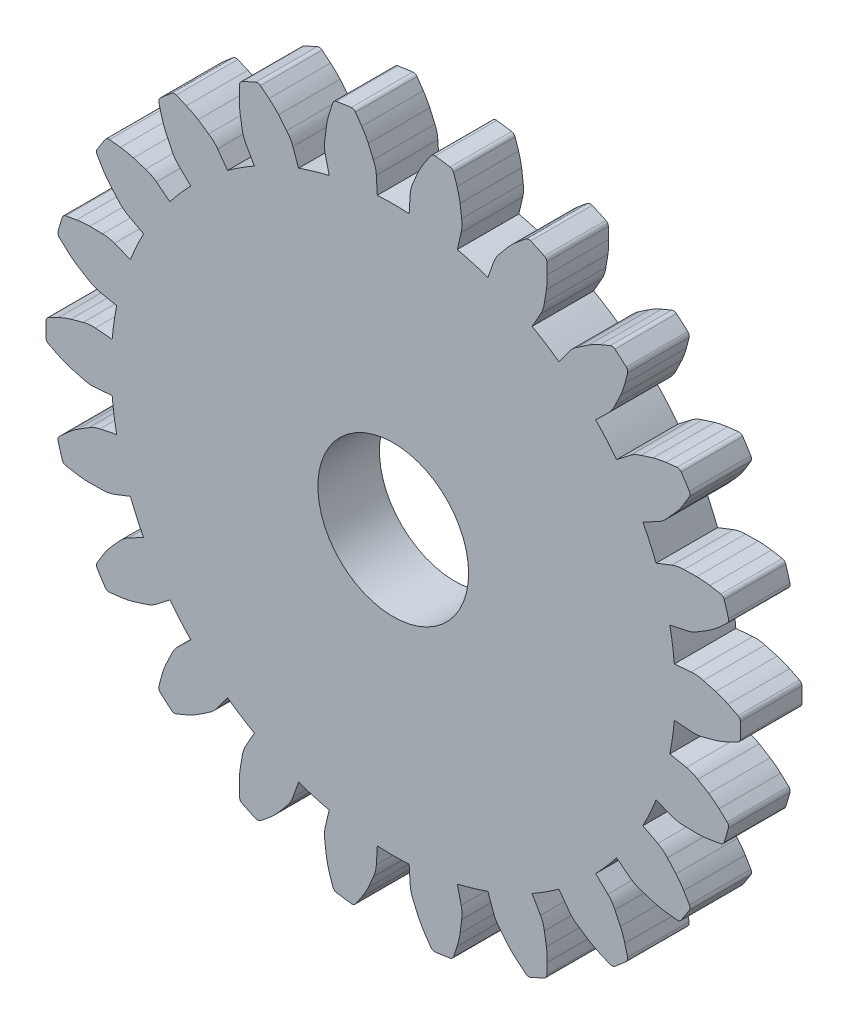
SolidWorks part; units mm, degrees
ref_plane "Front Plane" through (0, 0, 0) normal (0, 0, 1) x (1, 0, 0)
ref_plane "Top Plane" through (0, 0, 0) normal (0, 1, 0) x (1, 0, 0)
ref_plane "Right Plane" through (0, 0, 0) normal (1, 0, 0) x (0, 0, -1)
sketch "Model" plane through (0, 0, 0) normal (0, 0, 1) x (1, 0, 0)
  line L0 (21.4783, 13.1983) -> (22.0281, 13.2459)
  line L1 (21.4783, 11.617) -> (22.0281, 11.5695)
  line L2 (21.3309, 10.5918) -> (21.8719, 10.4825)
  line L3 (20.8854, 9.0746) -> (21.3996, 8.874)
  line L4 (20.4551, 8.1324) -> (20.9434, 7.8751)
  line L5 (19.6003, 6.8021) -> (20.0371, 6.4649)
  line L6 (18.9219, 6.0193) -> (19.3179, 5.6349)
  line L7 (17.7269, 4.9838) -> (18.051, 4.5372)
  line L8 (16.8555, 4.4238) -> (17.1272, 3.9435)
  line L9 (15.4172, 3.7669) -> (15.6023, 3.2471)
  line L10 (14.4233, 3.4751) -> (14.5486, 2.9377)
  line L11 (12.8582, 3.2501) -> (12.8893, 2.6991)
  line L12 (11.8223, 3.2501) -> (11.7912, 2.6991)
  line L13 (10.2572, 3.4751) -> (10.1319, 2.9377)
  line L14 (9.2633, 3.7669) -> (9.0782, 3.2471)
  line L15 (7.825, 4.4238) -> (7.5533, 3.9435)
  line L16 (6.9536, 4.9838) -> (6.6295, 4.5372)
  line L17 (5.7586, 6.0193) -> (5.3626, 5.6349)
  line L18 (5.0802, 6.8021) -> (4.6434, 6.4649)
  line L19 (4.2254, 8.1324) -> (3.7371, 7.8751)
  line L20 (3.7951, 9.0746) -> (3.2809, 8.874)
  line L21 (3.3496, 10.5918) -> (2.8086, 10.4825)
  line L22 (3.2022, 11.617) -> (2.6524, 11.5695)
  line L23 (3.2022, 13.1983) -> (2.6524, 13.2459)
  line L24 (3.3496, 14.2236) -> (2.8086, 14.3328)
  line L25 (3.7951, 15.7408) -> (3.2809, 15.9413)
  line L26 (4.2254, 16.683) -> (3.7371, 16.9402)
  line L27 (5.0802, 18.0132) -> (4.6434, 18.3505)
  line L28 (5.7586, 18.796) -> (5.3626, 19.1804)
  line L29 (6.9536, 19.8315) -> (6.6295, 20.2782)
  line L30 (7.825, 20.3915) -> (7.5533, 20.8719)
  line L31 (9.2633, 21.0484) -> (9.0782, 21.5683)
  line L32 (10.2572, 21.3402) -> (10.1319, 21.8777)
  line L33 (11.8223, 21.5653) -> (11.7912, 22.1162)
  line L34 (12.8582, 21.5653) -> (12.8893, 22.1162)
  line L35 (14.4233, 21.3402) -> (14.5486, 21.8777)
  line L36 (15.4172, 21.0484) -> (15.6023, 21.5683)
  line L37 (16.8555, 20.3915) -> (17.1272, 20.8719)
  line L38 (17.7269, 19.8315) -> (18.051, 20.2782)
  line L39 (18.9219, 18.796) -> (19.3179, 19.1804)
  line L40 (19.6003, 18.0132) -> (20.0371, 18.3505)
  line L41 (20.4551, 16.683) -> (20.9434, 16.9402)
  line L42 (20.8854, 15.7408) -> (21.3996, 15.9413)
  line L43 (21.3309, 14.2236) -> (21.8719, 14.3328)
  arc A0 (21.4783, 13.1983) -> (21.4191, 13.713) centre (12.3402, 12.4077) ccw
  arc A1 (22.4241, 13.2042) -> (22.0281, 13.2459) centre (22.1185, 12.2011) ccw
  arc A2 (22.8242, 13.0956) -> (22.4241, 13.2042) centre (-311.3875, -1217.0562) ccw
  arc A3 (23.225, 12.9388) -> (22.8242, 13.0956) centre (22.0063, 10.4144) ccw
  arc A4 (23.5458, 12.7799) -> (23.225, 12.9388) centre (15.9051, -2.2405) ccw
  arc A5 (23.6291, 12.4077) -> (23.6265, 12.6514) centre (12.3402, 12.4077) ccw
  arc A6 (23.6265, 12.6514) -> (23.5458, 12.7799) centre (23.4788, 12.6482) ccw
  arc A7 (21.4191, 11.1023) -> (21.4783, 11.617) centre (12.3402, 12.4077) ccw
  arc A8 (22.0281, 11.5695) -> (22.4241, 11.6111) centre (22.1185, 12.6143) ccw
  arc A9 (22.4241, 11.6111) -> (22.8242, 11.7197) centre (-311.3875, 1241.8716) ccw
  arc A10 (22.8242, 11.7197) -> (23.225, 11.8765) centre (22.0063, 14.4009) ccw
  arc A11 (23.225, 11.8765) -> (23.5458, 12.0354) centre (15.9051, 27.0558) ccw
  arc A12 (23.6265, 12.164) -> (23.6291, 12.4077) centre (12.3402, 12.4077) ccw
  arc A13 (23.5458, 12.0354) -> (23.6265, 12.164) centre (23.4788, 12.1671) ccw
  arc A14 (21.3309, 10.5918) -> (21.4191, 11.1023) centre (12.3402, 12.4077) ccw
  arc A15 (22.2401, 10.331) -> (21.8719, 10.4825) centre (21.6642, 9.4546) ccw
  arc A16 (22.5933, 10.1141) -> (22.2401, 10.331) centre (-644.6543, -1076.0497) ccw
  arc A17 (22.9337, 9.8507) -> (22.5933, 10.1141) centre (21.0532, 7.7719) ccw
  arc A18 (23.1967, 9.6079) -> (22.9337, 9.8507) centre (11.6338, -2.6515) ccw
  arc A19 (23.1719, 9.2272) -> (23.238, 9.4618) centre (12.3402, 12.4077) ccw
  arc A20 (23.238, 9.4618) -> (23.1967, 9.6079) centre (23.0953, 9.5004) ccw
  arc A21 (20.6836, 8.5974) -> (20.8854, 9.0746) centre (12.3402, 12.4077) ccw
  arc A22 (21.3996, 8.874) -> (21.7912, 8.8024) centre (21.7806, 9.851) ccw
  arc A23 (21.7912, 8.8024) -> (22.2057, 8.7939) centre (48.1057, 1283.2743) ccw
  arc A24 (22.2057, 8.7939) -> (22.6344, 8.8315) centre (22.1763, 11.5969) ccw
  arc A25 (22.6344, 8.8315) -> (22.987, 8.8936) centre (19.8876, 25.4581) ccw
  arc A26 (23.1007, 8.9941) -> (23.1719, 9.2272) centre (12.3402, 12.4077) ccw
  arc A27 (22.987, 8.8936) -> (23.1007, 8.9941) centre (22.9598, 9.0388) ccw
  arc A28 (20.4551, 8.1324) -> (20.6836, 8.5974) centre (12.3402, 12.4077) ccw
  arc A29 (21.254, 7.626) -> (20.9434, 7.8751) centre (20.4545, 6.9473) ccw
  arc A30 (21.5318, 7.3184) -> (21.254, 7.626) centre (-924.6953, -846.8627) ccw
  arc A31 (21.7842, 6.9698) -> (21.5318, 7.3184) centre (19.3942, 5.505) ccw
  arc A32 (21.9682, 6.6626) -> (21.7842, 6.9698) centre (7.4198, -1.8425) ccw
  arc A33 (21.8371, 6.3044) -> (21.9666, 6.5109) centre (12.3402, 12.4077) ccw
  arc A34 (21.9666, 6.5109) -> (21.9682, 6.6626) centre (21.8406, 6.5881) ccw
  arc A35 (19.2722, 6.4011) -> (19.6003, 6.8021) centre (12.3402, 12.4077) ccw
  arc A36 (20.0371, 6.4649) -> (20.3927, 6.2858) centre (20.6779, 7.2949) ccw
  arc A37 (20.3927, 6.2858) -> (20.788, 6.1609) centre (404.7015, 1221.719) ccw
  arc A38 (20.788, 6.1609) -> (21.2099, 6.0761) centre (21.5495, 8.8586) ccw
  arc A39 (21.2099, 6.0761) -> (21.5657, 6.0364) centre (23.2586, 22.8032) ccw
  arc A40 (21.7031, 6.1008) -> (21.8371, 6.3044) centre (12.3402, 12.4077) ccw
  arc A41 (21.5657, 6.0364) -> (21.7031, 6.1008) centre (21.5805, 6.1834) ccw
  arc A42 (18.9219, 6.0193) -> (19.2722, 6.4011) centre (12.3402, 12.4077) ccw
  arc A43 (19.5458, 5.3084) -> (19.3179, 5.6349) centre (18.5875, 4.8825) ccw
  arc A44 (19.7257, 4.9349) -> (19.5458, 5.3084) centre (-1128.8232, -548.0628) ccw
  arc A45 (19.8696, 4.5294) -> (19.7257, 4.9349) centre (17.1638, 3.7973) ccw
  arc A46 (19.9596, 4.1829) -> (19.8696, 4.5294) centre (3.6044, 0.121) ccw
  arc A47 (19.7329, 3.8761) -> (19.9154, 4.0377) centre (12.3402, 12.4077) ccw
  arc A48 (19.9154, 4.0377) -> (19.9596, 4.1829) centre (19.8162, 4.1472) ccw
  arc A49 (17.2991, 4.6915) -> (17.7269, 4.9838) centre (12.3402, 12.4077) ccw
  arc A50 (18.051, 4.5372) -> (18.3418, 4.2651) centre (18.8998, 5.153) ccw
  arc A51 (18.3418, 4.2651) -> (18.6859, 4.0339) centre (729.5104, 1062.1924) ccw
  arc A52 (18.6859, 4.0339) -> (19.0668, 3.8337) centre (20.1765, 6.4078) ccw
  arc A53 (19.0668, 3.8337) -> (19.397, 3.6953) centre (25.7451, 19.306) ccw
  arc A54 (19.547, 3.7185) -> (19.7329, 3.8761) centre (12.3402, 12.4077) ccw
  arc A55 (19.397, 3.6953) -> (19.547, 3.7185) centre (19.4527, 3.8322) ccw
  arc A56 (16.8555, 4.4238) -> (17.2991, 4.6915) centre (12.3402, 12.4077) ccw
  arc A57 (17.2538, 3.566) -> (17.1272, 3.9435) centre (16.2144, 3.4272) ccw
  arc A58 (17.3212, 3.1569) -> (17.2538, 3.566) centre (-1240.5008, -203.8569) ccw
  arc A59 (17.3451, 2.7272) -> (17.3212, 3.1569) centre (14.5426, 2.7871) ccw
  arc A60 (17.3338, 2.3694) -> (17.3451, 2.7272) centre (0.4967, 3.0799) ccw
  arc A61 (17.0298, 2.1389) -> (17.2504, 2.2426) centre (12.3402, 12.4077) ccw
  arc A62 (17.2504, 2.2426) -> (17.3338, 2.3694) centre (17.1861, 2.3756) ccw
  arc A63 (14.9244, 3.607) -> (15.4172, 3.7669) centre (12.3402, 12.4077) ccw
  arc A64 (15.6023, 3.2471) -> (15.8047, 2.9042) centre (16.5902, 3.5989) ccw
  arc A65 (15.8047, 2.9042) -> (16.0697, 2.5854) centre (996.2186, 817.6186) ccw
  arc A66 (16.0697, 2.5854) -> (16.3788, 2.2859) centre (18.1688, 4.4431) ccw
  arc A67 (16.3788, 2.2859) -> (16.6566, 2.0601) centre (27.1456, 15.25) ccw
  arc A68 (16.807, 2.0401) -> (17.0298, 2.1389) centre (12.3402, 12.4077) ccw
  arc A69 (16.6566, 2.0601) -> (16.807, 2.0401) centre (16.7486, 2.1758) ccw
  arc A70 (14.4233, 3.4751) -> (14.9244, 3.607) centre (12.3402, 12.4077) ccw
  arc A71 (14.5638, 2.5398) -> (14.5486, 2.9377) centre (13.5274, 2.6995) ccw
  arc A72 (14.5132, 2.1283) -> (14.5638, 2.5398) centre (-1250.6808, 157.8694) ccw
  arc A73 (14.415, 1.7093) -> (14.5132, 2.1283) centre (11.7429, 2.5563) ccw
  arc A74 (14.3034, 1.3692) -> (14.415, 1.7093) centre (-1.6515, 6.7944) ccw
  arc A75 (13.9468, 1.2337) -> (14.1877, 1.271) centre (12.3402, 12.4077) ccw
  arc A76 (14.1877, 1.271) -> (14.3034, 1.3692) centre (14.1635, 1.4167) ccw
  arc A77 (12.3402, 3.2354) -> (12.8582, 3.2501) centre (12.3402, 12.4077) ccw
  arc A78 (12.8893, 2.6991) -> (12.9869, 2.3131) centre (13.9363, 2.7583) ccw
  arc A79 (12.9869, 2.3131) -> (13.1513, 1.9325) centre (1183.2187, 507.8113) ccw
  arc A80 (13.1513, 1.9325) -> (13.3636, 1.5581) centre (15.6888, 3.1237) ccw
  arc A81 (13.3636, 1.5581) -> (13.5665, 1.2632) centre (27.3466, 10.9637) ccw
  arc A82 (13.7052, 1.2016) -> (13.9468, 1.2337) centre (12.3402, 12.4077) ccw
  arc A83 (13.5665, 1.2632) -> (13.7052, 1.2016) centre (13.6874, 1.3483) ccw
  arc A84 (11.8223, 3.2501) -> (12.3402, 3.2354) centre (12.3402, 12.4077) ccw
  arc A85 (11.6936, 2.3131) -> (11.7912, 2.6991) centre (10.7442, 2.7583) ccw
  arc A86 (11.5292, 1.9325) -> (11.6936, 2.3131) centre (-1158.5382, 507.8113) ccw
  arc A87 (11.3169, 1.5581) -> (11.5292, 1.9325) centre (8.9917, 3.1237) ccw
  arc A88 (11.114, 1.2632) -> (11.3169, 1.5581) centre (-2.6661, 10.9637) ccw
  arc A89 (10.7337, 1.2337) -> (10.9753, 1.2016) centre (12.3402, 12.4077) ccw
  arc A90 (10.9753, 1.2016) -> (11.114, 1.2632) centre (10.9931, 1.3483) ccw
  arc A91 (9.7561, 3.607) -> (10.2572, 3.4751) centre (12.3402, 12.4077) ccw
  arc A92 (10.1319, 2.9377) -> (10.1167, 2.5398) centre (11.1531, 2.6995) ccw
  arc A93 (10.1167, 2.5398) -> (10.1673, 2.1283) centre (1275.3613, 157.8694) ccw
  arc A94 (10.1673, 2.1283) -> (10.2655, 1.7093) centre (12.9376, 2.5563) ccw
  arc A95 (10.2655, 1.7093) -> (10.3771, 1.3692) centre (26.332, 6.7944) ccw
  arc A96 (10.4928, 1.271) -> (10.7337, 1.2337) centre (12.3402, 12.4077) ccw
  arc A97 (10.3771, 1.3692) -> (10.4928, 1.271) centre (10.517, 1.4167) ccw
  arc A98 (9.2633, 3.7669) -> (9.7561, 3.607) centre (12.3402, 12.4077) ccw
  arc A99 (8.8758, 2.9042) -> (9.0782, 3.2471) centre (8.0903, 3.5989) ccw
  arc A100 (8.6108, 2.5854) -> (8.8758, 2.9042) centre (-971.5381, 817.6186) ccw
  arc A101 (8.3017, 2.2859) -> (8.6108, 2.5854) centre (6.5117, 4.4431) ccw
  arc A102 (8.0239, 2.0601) -> (8.3017, 2.2859) centre (-2.4651, 15.25) ccw
  arc A103 (7.6507, 2.1389) -> (7.8735, 2.0401) centre (12.3402, 12.4077) ccw
  arc A104 (7.8735, 2.0401) -> (8.0239, 2.0601) centre (7.9319, 2.1758) ccw
  arc A105 (7.3814, 4.6915) -> (7.825, 4.4238) centre (12.3402, 12.4077) ccw
  arc A106 (7.5533, 3.9435) -> (7.4267, 3.566) centre (8.4661, 3.4272) ccw
  arc A107 (7.4267, 3.566) -> (7.3593, 3.1569) centre (1265.1813, -203.8569) ccw
  arc A108 (7.3593, 3.1569) -> (7.3354, 2.7272) centre (10.1379, 2.7871) ccw
  arc A109 (7.3354, 2.7272) -> (7.3467, 2.3694) centre (24.1838, 3.0799) ccw
  arc A110 (7.4301, 2.2426) -> (7.6507, 2.1389) centre (12.3402, 12.4077) ccw
  arc A111 (7.3467, 2.3694) -> (7.4301, 2.2426) centre (7.4944, 2.3756) ccw
  arc A112 (6.9536, 4.9838) -> (7.3814, 4.6915) centre (12.3402, 12.4077) ccw
  arc A113 (6.3387, 4.2651) -> (6.6295, 4.5372) centre (5.7807, 5.153) ccw
  arc A114 (5.9946, 4.0339) -> (6.3387, 4.2651) centre (-704.83, 1062.1924) ccw
  arc A115 (5.6137, 3.8337) -> (5.9946, 4.0339) centre (4.504, 6.4078) ccw
  arc A116 (5.2835, 3.6953) -> (5.6137, 3.8337) centre (-1.0646, 19.306) ccw
  arc A117 (4.9476, 3.8761) -> (5.1335, 3.7185) centre (12.3402, 12.4077) ccw
  arc A118 (5.1335, 3.7185) -> (5.2835, 3.6953) centre (5.2278, 3.8322) ccw
  arc A119 (5.4083, 6.4011) -> (5.7586, 6.0193) centre (12.3402, 12.4077) ccw
  arc A120 (5.3626, 5.6349) -> (5.1347, 5.3084) centre (6.093, 4.8825) ccw
  arc A121 (5.1347, 5.3084) -> (4.9548, 4.9349) centre (1153.5037, -548.0628) ccw
  arc A122 (4.9548, 4.9349) -> (4.8109, 4.5294) centre (7.5167, 3.7973) ccw
  arc A123 (4.8109, 4.5294) -> (4.7209, 4.1829) centre (21.0761, 0.121) ccw
  arc A124 (4.7651, 4.0377) -> (4.9476, 3.8761) centre (12.3402, 12.4077) ccw
  arc A125 (4.7209, 4.1829) -> (4.7651, 4.0377) centre (4.8643, 4.1472) ccw
  arc A126 (5.0802, 6.8021) -> (5.4083, 6.4011) centre (12.3402, 12.4077) ccw
  arc A127 (4.2878, 6.2858) -> (4.6434, 6.4649) centre (4.0026, 7.2949) ccw
  arc A128 (3.8925, 6.1609) -> (4.2878, 6.2858) centre (-380.021, 1221.719) ccw
  arc A129 (3.4706, 6.0761) -> (3.8925, 6.1609) centre (3.131, 8.8586) ccw
  arc A130 (3.1148, 6.0364) -> (3.4706, 6.0761) centre (1.4219, 22.8032) ccw
  arc A131 (2.8434, 6.3044) -> (2.9774, 6.1008) centre (12.3402, 12.4077) ccw
  arc A132 (2.9774, 6.1008) -> (3.1148, 6.0364) centre (3.1, 6.1834) ccw
  arc A133 (3.9969, 8.5974) -> (4.2254, 8.1324) centre (12.3402, 12.4077) ccw
  arc A134 (3.7371, 7.8751) -> (3.4265, 7.626) centre (4.226, 6.9473) ccw
  arc A135 (3.4265, 7.626) -> (3.1487, 7.3184) centre (949.3758, -846.8627) ccw
  arc A136 (3.1487, 7.3184) -> (2.8963, 6.9698) centre (5.2863, 5.505) ccw
  arc A137 (2.8963, 6.9698) -> (2.7123, 6.6626) centre (17.2607, -1.8425) ccw
  arc A138 (2.7139, 6.5109) -> (2.8434, 6.3044) centre (12.3402, 12.4077) ccw
  arc A139 (2.7123, 6.6626) -> (2.7139, 6.5109) centre (2.8399, 6.5881) ccw
  arc A140 (3.7951, 9.0746) -> (3.9969, 8.5974) centre (12.3402, 12.4077) ccw
  arc A141 (2.8893, 8.8024) -> (3.2809, 8.874) centre (2.8999, 9.851) ccw
  arc A142 (2.4748, 8.7939) -> (2.8893, 8.8024) centre (-23.4252, 1283.2743) ccw
  arc A143 (2.0461, 8.8315) -> (2.4748, 8.7939) centre (2.5042, 11.5969) ccw
  arc A144 (1.6935, 8.8936) -> (2.0461, 8.8315) centre (4.7929, 25.4581) ccw
  arc A145 (1.5086, 9.2272) -> (1.5798, 8.9941) centre (12.3402, 12.4077) ccw
  arc A146 (1.5798, 8.9941) -> (1.6935, 8.8936) centre (1.7207, 9.0388) ccw
  arc A147 (3.2614, 11.1023) -> (3.3496, 10.5918) centre (12.3402, 12.4077) ccw
  arc A148 (2.8086, 10.4825) -> (2.4404, 10.331) centre (3.0163, 9.4546) ccw
  arc A149 (2.4404, 10.331) -> (2.0872, 10.1141) centre (669.3348, -1076.0497) ccw
  arc A150 (2.0872, 10.1141) -> (1.7468, 9.8507) centre (3.6273, 7.7719) ccw
  arc A151 (1.7468, 9.8507) -> (1.4838, 9.6079) centre (13.0467, -2.6515) ccw
  arc A152 (1.4425, 9.4618) -> (1.5086, 9.2272) centre (12.3402, 12.4077) ccw
  arc A153 (1.4838, 9.6079) -> (1.4425, 9.4618) centre (1.5852, 9.5004) ccw
  arc A154 (3.2022, 11.617) -> (3.2614, 11.1023) centre (12.3402, 12.4077) ccw
  arc A155 (2.2564, 11.6111) -> (2.6524, 11.5695) centre (2.562, 12.6143) ccw
  arc A156 (1.8563, 11.7197) -> (2.2564, 11.6111) centre (336.068, 1241.8716) ccw
  arc A157 (1.4555, 11.8765) -> (1.8563, 11.7197) centre (2.6742, 14.4009) ccw
  arc A158 (1.1347, 12.0354) -> (1.4555, 11.8765) centre (8.7754, 27.0558) ccw
  arc A159 (1.0514, 12.4077) -> (1.054, 12.164) centre (12.3402, 12.4077) ccw
  arc A160 (1.054, 12.164) -> (1.1347, 12.0354) centre (1.2017, 12.1671) ccw
  arc A161 (3.2614, 13.713) -> (3.2022, 13.1983) centre (12.3402, 12.4077) ccw
  arc A162 (2.6524, 13.2459) -> (2.2564, 13.2042) centre (2.562, 12.2011) ccw
  arc A163 (2.2564, 13.2042) -> (1.8563, 13.0956) centre (336.068, -1217.0562) ccw
  arc A164 (1.8563, 13.0956) -> (1.4555, 12.9388) centre (2.6742, 10.4144) ccw
  arc A165 (1.4555, 12.9388) -> (1.1347, 12.7799) centre (8.7754, -2.2405) ccw
  arc A166 (1.054, 12.6514) -> (1.0514, 12.4077) centre (12.3402, 12.4077) ccw
  arc A167 (1.1347, 12.7799) -> (1.054, 12.6514) centre (1.2017, 12.6482) ccw
  arc A168 (3.3496, 14.2236) -> (3.2614, 13.713) centre (12.3402, 12.4077) ccw
  arc A169 (2.4404, 14.4843) -> (2.8086, 14.3328) centre (3.0163, 15.3607) ccw
  arc A170 (2.0872, 14.7013) -> (2.4404, 14.4843) centre (669.3348, 1100.865) ccw
  arc A171 (1.7468, 14.9646) -> (2.0872, 14.7013) centre (3.6273, 17.0434) ccw
  arc A172 (1.4838, 15.2075) -> (1.7468, 14.9646) centre (13.0467, 27.4668) ccw
  arc A173 (1.5086, 15.5881) -> (1.4425, 15.3535) centre (12.3402, 12.4077) ccw
  arc A174 (1.4425, 15.3535) -> (1.4838, 15.2075) centre (1.5852, 15.315) ccw
  arc A175 (3.9969, 16.2179) -> (3.7951, 15.7408) centre (12.3402, 12.4077) ccw
  arc A176 (3.2809, 15.9413) -> (2.8893, 16.0129) centre (2.8999, 14.9643) ccw
  arc A177 (2.8893, 16.0129) -> (2.4748, 16.0214) centre (-23.4252, -1258.459) ccw
  arc A178 (2.4748, 16.0214) -> (2.0461, 15.9839) centre (2.5042, 13.2184) ccw
  arc A179 (2.0461, 15.9839) -> (1.6935, 15.9218) centre (4.7929, -0.6428) ccw
  arc A180 (1.5798, 15.8212) -> (1.5086, 15.5881) centre (12.3402, 12.4077) ccw
  arc A181 (1.6935, 15.9218) -> (1.5798, 15.8212) centre (1.7207, 15.7765) ccw
  arc A182 (4.2254, 16.683) -> (3.9969, 16.2179) centre (12.3402, 12.4077) ccw
  arc A183 (3.4265, 17.1893) -> (3.7371, 16.9402) centre (4.226, 17.868) ccw
  arc A184 (3.1487, 17.497) -> (3.4265, 17.1893) centre (949.3758, 871.6781) ccw
  arc A185 (2.8963, 17.8456) -> (3.1487, 17.497) centre (5.2863, 19.3103) ccw
  arc A186 (2.7123, 18.1527) -> (2.8963, 17.8456) centre (17.2607, 26.6578) ccw
  arc A187 (2.8434, 18.5109) -> (2.7139, 18.3045) centre (12.3402, 12.4077) ccw
  arc A188 (2.7139, 18.3045) -> (2.7123, 18.1527) centre (2.8399, 18.2273) ccw
  arc A189 (5.4083, 18.4142) -> (5.0802, 18.0132) centre (12.3402, 12.4077) ccw
  arc A190 (4.6434, 18.3505) -> (4.2878, 18.5295) centre (4.0026, 17.5204) ccw
  arc A191 (4.2878, 18.5295) -> (3.8925, 18.6544) centre (-380.021, -1196.9036) ccw
  arc A192 (3.8925, 18.6544) -> (3.4706, 18.7392) centre (3.131, 15.9567) ccw
  arc A193 (3.4706, 18.7392) -> (3.1148, 18.779) centre (1.4219, 2.0122) ccw
  arc A194 (2.9774, 18.7145) -> (2.8434, 18.5109) centre (12.3402, 12.4077) ccw
  arc A195 (3.1148, 18.779) -> (2.9774, 18.7145) centre (3.1, 18.6319) ccw
  arc A196 (5.7586, 18.796) -> (5.4083, 18.4142) centre (12.3402, 12.4077) ccw
  arc A197 (5.1347, 19.5069) -> (5.3626, 19.1804) centre (6.093, 19.9329) ccw
  arc A198 (4.9548, 19.8804) -> (5.1347, 19.5069) centre (1153.5037, 572.8782) ccw
  arc A199 (4.8109, 20.286) -> (4.9548, 19.8804) centre (7.5167, 21.0181) ccw
  arc A200 (4.7209, 20.6325) -> (4.8109, 20.286) centre (21.0761, 24.6943) ccw
  arc A201 (4.9476, 20.9392) -> (4.7651, 20.7777) centre (12.3402, 12.4077) ccw
  arc A202 (4.7651, 20.7777) -> (4.7209, 20.6325) centre (4.8643, 20.6681) ccw
  arc A203 (7.3814, 20.1238) -> (6.9536, 19.8315) centre (12.3402, 12.4077) ccw
  arc A204 (6.6295, 20.2782) -> (6.3387, 20.5502) centre (5.7807, 19.6623) ccw
  arc A205 (6.3387, 20.5502) -> (5.9946, 20.7814) centre (-704.83, -1037.3771) ccw
  arc A206 (5.9946, 20.7814) -> (5.6137, 20.9816) centre (4.504, 18.4075) ccw
  arc A207 (5.6137, 20.9816) -> (5.2835, 21.12) centre (-1.0646, 5.5093) ccw
  arc A208 (5.1335, 21.0968) -> (4.9476, 20.9392) centre (12.3402, 12.4077) ccw
  arc A209 (5.2835, 21.12) -> (5.1335, 21.0968) centre (5.2278, 20.9831) ccw
  arc A210 (7.825, 20.3915) -> (7.3814, 20.1238) centre (12.3402, 12.4077) ccw
  arc A211 (7.4267, 21.2494) -> (7.5533, 20.8719) centre (8.4661, 21.3881) ccw
  arc A212 (7.3593, 21.6584) -> (7.4267, 21.2494) centre (1265.1813, 228.6723) ccw
  arc A213 (7.3354, 22.0881) -> (7.3593, 21.6584) centre (10.1379, 22.0282) ccw
  arc A214 (7.3467, 22.4459) -> (7.3354, 22.0881) centre (24.1838, 21.7354) ccw
  arc A215 (7.6507, 22.6764) -> (7.4301, 22.5728) centre (12.3402, 12.4077) ccw
  arc A216 (7.4301, 22.5728) -> (7.3467, 22.4459) centre (7.4944, 22.4397) ccw
  arc A217 (9.7561, 21.2083) -> (9.2633, 21.0484) centre (12.3402, 12.4077) ccw
  arc A218 (9.0782, 21.5683) -> (8.8758, 21.9112) centre (8.0903, 21.2165) ccw
  arc A219 (8.8758, 21.9112) -> (8.6108, 22.23) centre (-971.5381, -792.8033) ccw
  arc A220 (8.6108, 22.23) -> (8.3017, 22.5294) centre (6.5117, 20.3722) ccw
  arc A221 (8.3017, 22.5294) -> (8.0239, 22.7552) centre (-2.4651, 9.5653) ccw
  arc A222 (7.8735, 22.7752) -> (7.6507, 22.6764) centre (12.3402, 12.4077) ccw
  arc A223 (8.0239, 22.7552) -> (7.8735, 22.7752) centre (7.9319, 22.6395) ccw
  arc A224 (10.2572, 21.3402) -> (9.7561, 21.2083) centre (12.3402, 12.4077) ccw
  arc A225 (10.1167, 22.2755) -> (10.1319, 21.8777) centre (11.1531, 22.1158) ccw
  arc A226 (10.1673, 22.687) -> (10.1167, 22.2755) centre (1275.3613, -133.0541) ccw
  arc A227 (10.2655, 23.106) -> (10.1673, 22.687) centre (12.9376, 22.259) ccw
  arc A228 (10.3771, 23.4462) -> (10.2655, 23.106) centre (26.332, 18.0209) ccw
  arc A229 (10.7337, 23.5817) -> (10.4928, 23.5444) centre (12.3402, 12.4077) ccw
  arc A230 (10.4928, 23.5444) -> (10.3771, 23.4462) centre (10.517, 23.3986) ccw
  arc A231 (12.3402, 21.5799) -> (11.8223, 21.5653) centre (12.3402, 12.4077) ccw
  arc A232 (11.7912, 22.1162) -> (11.6936, 22.5023) centre (10.7442, 22.057) ccw
  arc A233 (11.6936, 22.5023) -> (11.5292, 22.8828) centre (-1158.5382, -482.996) ccw
  arc A234 (11.5292, 22.8828) -> (11.3169, 23.2572) centre (8.9917, 21.6917) ccw
  arc A235 (11.3169, 23.2572) -> (11.114, 23.5521) centre (-2.6661, 13.8516) ccw
  arc A236 (10.9753, 23.6137) -> (10.7337, 23.5817) centre (12.3402, 12.4077) ccw
  arc A237 (11.114, 23.5521) -> (10.9753, 23.6137) centre (10.9931, 23.467) ccw
  arc A238 (12.8582, 21.5653) -> (12.3402, 21.5799) centre (12.3402, 12.4077) ccw
  arc A239 (12.9869, 22.5023) -> (12.8893, 22.1162) centre (13.9363, 22.057) ccw
  arc A240 (13.1513, 22.8828) -> (12.9869, 22.5023) centre (1183.2187, -482.996) ccw
  arc A241 (13.3636, 23.2572) -> (13.1513, 22.8828) centre (15.6888, 21.6917) ccw
  arc A242 (13.5665, 23.5521) -> (13.3636, 23.2572) centre (27.3466, 13.8516) ccw
  arc A243 (13.9468, 23.5817) -> (13.7052, 23.6137) centre (12.3402, 12.4077) ccw
  arc A244 (13.7052, 23.6137) -> (13.5665, 23.5521) centre (13.6874, 23.467) ccw
  arc A245 (14.9244, 21.2083) -> (14.4233, 21.3402) centre (12.3402, 12.4077) ccw
  arc A246 (14.5486, 21.8777) -> (14.5638, 22.2755) centre (13.5274, 22.1158) ccw
  arc A247 (14.5638, 22.2755) -> (14.5132, 22.687) centre (-1250.6808, -133.0541) ccw
  arc A248 (14.5132, 22.687) -> (14.415, 23.106) centre (11.7429, 22.259) ccw
  arc A249 (14.415, 23.106) -> (14.3034, 23.4462) centre (-1.6515, 18.0209) ccw
  arc A250 (14.1877, 23.5444) -> (13.9468, 23.5817) centre (12.3402, 12.4077) ccw
  arc A251 (14.3034, 23.4462) -> (14.1877, 23.5444) centre (14.1635, 23.3986) ccw
  arc A252 (15.4172, 21.0484) -> (14.9244, 21.2083) centre (12.3402, 12.4077) ccw
  arc A253 (15.8047, 21.9112) -> (15.6023, 21.5683) centre (16.5902, 21.2165) ccw
  arc A254 (16.0697, 22.23) -> (15.8047, 21.9112) centre (996.2186, -792.8033) ccw
  arc A255 (16.3788, 22.5294) -> (16.0697, 22.23) centre (18.1688, 20.3722) ccw
  arc A256 (16.6566, 22.7552) -> (16.3788, 22.5294) centre (27.1456, 9.5653) ccw
  arc A257 (17.0298, 22.6764) -> (16.807, 22.7752) centre (12.3402, 12.4077) ccw
  arc A258 (16.807, 22.7752) -> (16.6566, 22.7552) centre (16.7486, 22.6395) ccw
  arc A259 (17.2991, 20.1238) -> (16.8555, 20.3915) centre (12.3402, 12.4077) ccw
  arc A260 (17.1272, 20.8719) -> (17.2538, 21.2494) centre (16.2144, 21.3881) ccw
  arc A261 (17.2538, 21.2494) -> (17.3212, 21.6584) centre (-1240.5008, 228.6723) ccw
  arc A262 (17.3212, 21.6584) -> (17.3451, 22.0881) centre (14.5426, 22.0282) ccw
  arc A263 (17.3451, 22.0881) -> (17.3338, 22.4459) centre (0.4967, 21.7354) ccw
  arc A264 (17.2504, 22.5728) -> (17.0298, 22.6764) centre (12.3402, 12.4077) ccw
  arc A265 (17.3338, 22.4459) -> (17.2504, 22.5728) centre (17.1861, 22.4397) ccw
  arc A266 (17.7269, 19.8315) -> (17.2991, 20.1238) centre (12.3402, 12.4077) ccw
  arc A267 (18.3418, 20.5502) -> (18.051, 20.2782) centre (18.8998, 19.6623) ccw
  arc A268 (18.6859, 20.7814) -> (18.3418, 20.5502) centre (729.5104, -1037.3771) ccw
  arc A269 (19.0668, 20.9816) -> (18.6859, 20.7814) centre (20.1765, 18.4075) ccw
  arc A270 (19.397, 21.12) -> (19.0668, 20.9816) centre (25.7451, 5.5093) ccw
  arc A271 (19.7329, 20.9392) -> (19.547, 21.0968) centre (12.3402, 12.4077) ccw
  arc A272 (19.547, 21.0968) -> (19.397, 21.12) centre (19.4527, 20.9831) ccw
  arc A273 (19.2722, 18.4142) -> (18.9219, 18.796) centre (12.3402, 12.4077) ccw
  arc A274 (19.3179, 19.1804) -> (19.5458, 19.5069) centre (18.5875, 19.9329) ccw
  arc A275 (19.5458, 19.5069) -> (19.7257, 19.8804) centre (-1128.8232, 572.8782) ccw
  arc A276 (19.7257, 19.8804) -> (19.8696, 20.286) centre (17.1638, 21.0181) ccw
  arc A277 (19.8696, 20.286) -> (19.9596, 20.6325) centre (3.6044, 24.6943) ccw
  arc A278 (19.9154, 20.7777) -> (19.7329, 20.9392) centre (12.3402, 12.4077) ccw
  arc A279 (19.9596, 20.6325) -> (19.9154, 20.7777) centre (19.8162, 20.6681) ccw
  arc A280 (19.6003, 18.0132) -> (19.2722, 18.4142) centre (12.3402, 12.4077) ccw
  arc A281 (20.3927, 18.5295) -> (20.0371, 18.3505) centre (20.6779, 17.5204) ccw
  arc A282 (20.788, 18.6544) -> (20.3927, 18.5295) centre (404.7015, -1196.9036) ccw
  arc A283 (21.2099, 18.7392) -> (20.788, 18.6544) centre (21.5495, 15.9567) ccw
  arc A284 (21.5657, 18.779) -> (21.2099, 18.7392) centre (23.2586, 2.0122) ccw
  arc A285 (21.8371, 18.5109) -> (21.7031, 18.7145) centre (12.3402, 12.4077) ccw
  arc A286 (21.7031, 18.7145) -> (21.5657, 18.779) centre (21.5805, 18.6319) ccw
  arc A287 (20.6836, 16.2179) -> (20.4551, 16.683) centre (12.3402, 12.4077) ccw
  arc A288 (20.9434, 16.9402) -> (21.254, 17.1893) centre (20.4545, 17.868) ccw
  arc A289 (21.254, 17.1893) -> (21.5318, 17.497) centre (-924.6953, 871.6781) ccw
  arc A290 (21.5318, 17.497) -> (21.7842, 17.8456) centre (19.3942, 19.3103) ccw
  arc A291 (21.7842, 17.8456) -> (21.9682, 18.1527) centre (7.4198, 26.6578) ccw
  arc A292 (21.9666, 18.3045) -> (21.8371, 18.5109) centre (12.3402, 12.4077) ccw
  arc A293 (21.9682, 18.1527) -> (21.9666, 18.3045) centre (21.8406, 18.2273) ccw
  arc A294 (20.8854, 15.7408) -> (20.6836, 16.2179) centre (12.3402, 12.4077) ccw
  arc A295 (21.7912, 16.0129) -> (21.3996, 15.9413) centre (21.7806, 14.9643) ccw
  arc A296 (22.2057, 16.0214) -> (21.7912, 16.0129) centre (48.1057, -1258.459) ccw
  arc A297 (22.6344, 15.9839) -> (22.2057, 16.0214) centre (22.1763, 13.2184) ccw
  arc A298 (22.987, 15.9218) -> (22.6344, 15.9839) centre (19.8876, -0.6428) ccw
  arc A299 (23.1719, 15.5881) -> (23.1007, 15.8212) centre (12.3402, 12.4077) ccw
  arc A300 (23.1007, 15.8212) -> (22.987, 15.9218) centre (22.9598, 15.7765) ccw
  arc A301 (21.4191, 13.713) -> (21.3309, 14.2236) centre (12.3402, 12.4077) ccw
  arc A302 (21.8719, 14.3328) -> (22.2401, 14.4843) centre (21.6642, 15.3607) ccw
  arc A303 (22.2401, 14.4843) -> (22.5933, 14.7013) centre (-644.6543, 1100.865) ccw
  arc A304 (22.5933, 14.7013) -> (22.9337, 14.9646) centre (21.0532, 17.0434) ccw
  arc A305 (22.9337, 14.9646) -> (23.1967, 15.2075) centre (11.6338, 27.4668) ccw
  arc A306 (23.238, 15.3535) -> (23.1719, 15.5881) centre (12.3402, 12.4077) ccw
  arc A307 (23.1967, 15.2075) -> (23.238, 15.3535) centre (23.0953, 15.315) ccw
  circle A310 centre (12.3402, 12.4077) radius 2.45
  dimension "D1" = 4.9
extrude "Boss-Extrude1" add sketch "Model" along normal blind 2
